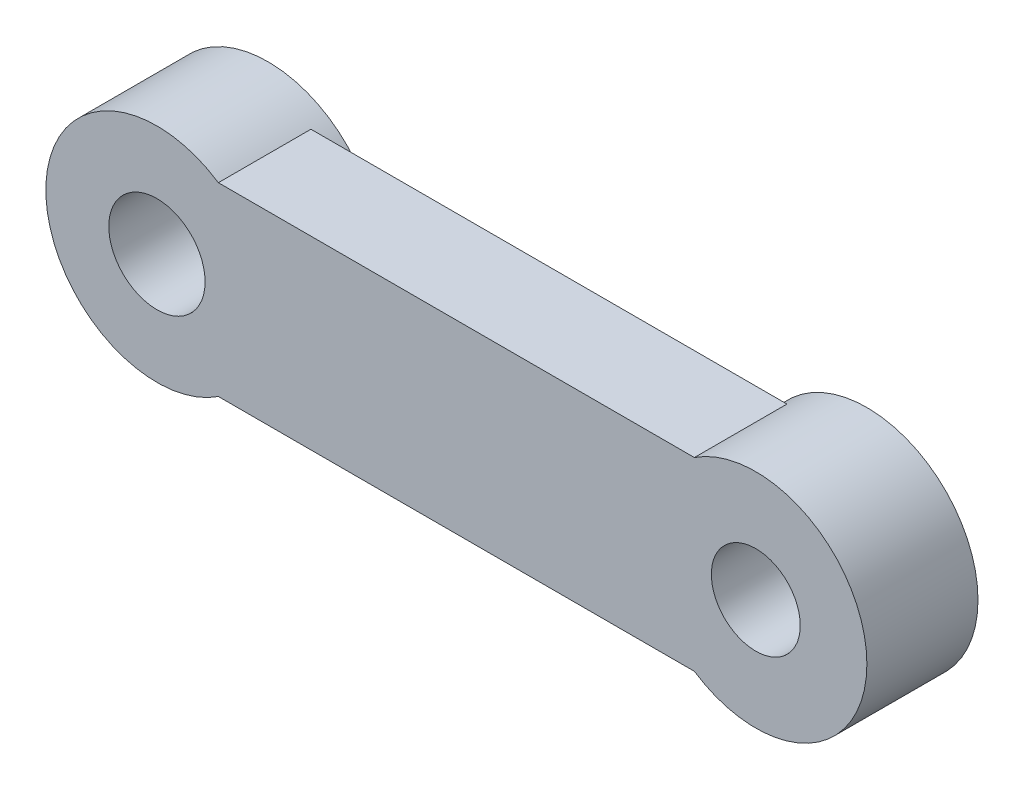
SolidWorks part; units mm, degrees
ref_plane "Front Plane" through (0, 0, 0) normal (0, 0, 1) x (1, 0, 0)
ref_plane "Top Plane" through (0, 0, 0) normal (0, 1, 0) x (1, 0, 0)
ref_plane "Right Plane" through (0, 0, 0) normal (1, 0, 0) x (0, 0, -1)
sketch "Sketch14" plane through (0, 0, 0) normal (0, 0, 1) x (1, 0, 0)
  line L0 (0, 2.5) -> (16.17, 2.5)
  line L1 (0, -2.5) -> (16.17, -2.5)
  circle A0 centre (0, 0) radius 1.3
  circle A1 centre (0, 0) radius 2.5
  circle A2 centre (16.17, 0) radius 1.2
  circle A3 centre (16.17, 0) radius 2.5
  dimension "D1" = 2.6
  dimension "D2" = 5
  dimension "D3" = 5
  dimension "D5" = 2.4
  dimension "D4" = 16.17
extrude "Boss-Extrude1" add sketch "Sketch14" along normal blind 2.5 separate body contours A3 L0 A1 L1 | A3 A2 | A1 A0
sketch "Sketch15" plane through (0, 0, 2.5) normal (0, 0, 1) x (1, 0, 0)
  circle A0 centre (16.17, 0) radius 3
  circle A1 centre (0, 0) radius 3
  circle A2 centre (0, 0) radius 1.3 construction
  circle A3 centre (16.17, 0) radius 1.2 construction
  circle A4 centre (0, 0) radius 1.3
  circle A5 centre (16.17, 0) radius 1.2
  dimension "D1" = 6
extrude "Boss-Extrude2" add sketch "Sketch15" against normal blind 3
